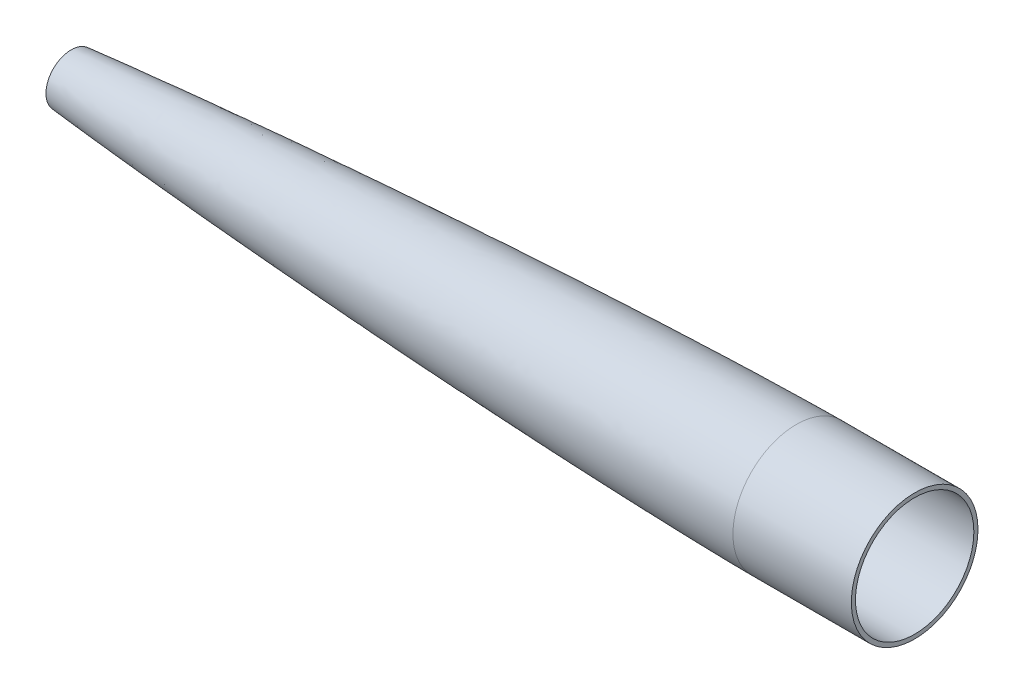
SolidWorks part; units mm, degrees
ref_plane "Front Plane" through (0, 0, 0) normal (0, 0, 1) x (1, 0, 0)
ref_plane "Top Plane" through (0, 0, 0) normal (0, 1, 0) x (1, 0, 0)
ref_plane "Right Plane" through (0, 0, 0) normal (1, 0, 0) x (0, 0, -1)
sketch "Sketch1" plane through (0, 0, 0) normal (0, 0, 1) x (1, 0, 0)
  line L0 (381, 27.178) -> (431.8, 27.178)
  line L1 (381, 25.4) -> (431.8, 25.4)
  line L2 (431.8, 27.178) -> (431.8, 25.4)
  line L3 (0, 0) -> (-1.5257, 0)
  line L4 (-1.5257, 0) -> (-1.5257, 0.9131)
  spline S0 degree 4 poles (0, 0) (0.0019, 0.0032) (0.0064, 0.0093) (0.0177, 0.0192) (0.0422, 0.0365) (0.0779, 0.0573) (0.1247, 0.0811) (0.1912, 0.1116) (0.271, 0.1447) (0.3911, 0.1908) (0.5706, 0.2533) (0.8326, 0.3363) (1.2601, 0.4592) (1.9831, 0.6462) (3.2808, 0.9439) (5.7051, 1.4307) (10.2743, 2.2232) (18.4903, 3.4427) (31.84, 5.1375) (49.7469, 7.0995) (71.1098, 9.1678) (94.2686, 11.1851) (117.4416, 13.0306) (140.6255, 14.7331) (163.8183, 16.3102) (187.0185, 17.7729) (210.2253, 19.1277) (239.2412, 20.6903) (268.266, 22.0787) (297.2989, 23.2863) (326.3397, 24.2853) (346.2421, 24.8431) (362.8124, 25.1993) (373.5739, 25.3501) (378.5246, 25.3942) (381, 25.4) knots 0 0 0 0 0 0.000039 0.000078 0.000157 0.000314 0.000471 0.000628 0.000923 0.001218 0.001818 0.002616 0.0038 0.005873 0.009633 0.01655 0.029679 0.054408 0.096565 0.157395 0.218224 0.279054 0.339884 0.400713 0.461543 0.522372 0.583202 0.644031 0.765691 0.82652 0.88735 0.948179 0.97409 1 1 1 1 1 construction
  spline S1 degree 4 poles (0, 0) (0.0019, 0.0032) (0.0064, 0.0093) (0.0177, 0.0192) (0.0422, 0.0365) (0.0779, 0.0573) (0.1247, 0.0811) (0.1912, 0.1116) (0.271, 0.1447) (0.3911, 0.1908) (0.5706, 0.2533) (0.8326, 0.3363) (1.2601, 0.4592) (1.9831, 0.6462) (3.2808, 0.9439) (5.7051, 1.4307) (10.2743, 2.2232) (18.4903, 3.4427) (31.84, 5.1375) (49.7469, 7.0995) (71.1098, 9.1678) (94.2686, 11.1851) (117.4416, 13.0306) (140.6255, 14.7331) (163.8183, 16.3102) (187.0185, 17.7729) (210.2253, 19.1277) (239.2412, 20.6903) (268.266, 22.0787) (297.2989, 23.2863) (326.3397, 24.2853) (346.2421, 24.8431) (362.8124, 25.1993) (373.5739, 25.3501) (378.5246, 25.3942) (381, 25.4) knots 0 0 0 0 0 0.000039 0.000078 0.000157 0.000314 0.000471 0.000628 0.000923 0.001218 0.001818 0.002616 0.0038 0.005873 0.009633 0.01655 0.029679 0.054408 0.096565 0.157395 0.218224 0.279054 0.339884 0.400713 0.461543 0.522372 0.583202 0.644031 0.765691 0.82652 0.88735 0.948179 0.97409 1 1 1 1 1
  spline S2 degree 1 poles (-1.5257, 0.9131) (381, 27.178) knots 0 0 1 1 construction
  spline S3 degree 3 poles (-1.5257, 0.9131) (-1.4569, 1.028) (-1.2638, 1.2699) (-1.0874, 1.4122) (-1.0135, 1.4682) (-0.9258, 1.5282) (-0.8554, 1.5714) (-0.781, 1.6138) (-0.7219, 1.6452) (-0.652, 1.6803) (-0.5784, 1.7149) (-0.5005, 1.7492) (-0.4055, 1.789) (-0.2986, 1.8307) (-0.1799, 1.8743) (-0.0293, 1.9267) (0.1485, 1.9847) (0.3542, 2.0477) (0.6217, 2.1254) (0.9478, 2.2143) (1.333, 2.3128) (1.8409, 2.4362) (2.4702, 2.5796) (3.2199, 2.7399) (4.2165, 2.9424) (5.4577, 3.1787) (6.9445, 3.4446) (8.4301, 3.6966) (9.9145, 3.9378) (11.8933, 4.2478) (14.3668, 4.6164) (17.3349, 5.0357) (20.3031, 5.4369) (24.2616, 5.9518) (29.2112, 6.5629) (35.1525, 7.2565) (41.0957, 7.9184) (49.0223, 8.7645) (58.9341, 9.764) (70.8331, 10.8911) (82.7362, 11.9575) (94.6427, 12.972) (106.5523, 13.9408) (122.4353, 15.1775) (142.2951, 16.629) (166.135, 18.2394) (189.9821, 19.7296) (213.8356, 21.1064) (245.6483, 22.7946) (285.4289, 24.6294) (325.227, 26.0608) (353.1023, 26.7817) (369.0324, 27.0705) (377.0118, 27.1686) (381, 27.178) knots 0 0 0 0 0.000031 0.000061 0.000092 0.000122 0.000183 0.000244 0.000305 0.000366 0.000488 0.00061 0.000732 0.000977 0.001221 0.001465 0.001953 0.002441 0.00293 0.003906 0.004883 0.005859 0.007813 0.009766 0.011719 0.015625 0.019531 0.023438 0.027344 0.03125 0.039063 0.046876 0.054688 0.062501 0.078126 0.093751 0.109376 0.125001 0.156252 0.187502 0.218752 0.250003 0.281253 0.312503 0.375004 0.437505 0.500005 0.562506 0.625007 0.750008 0.87501 0.93751 0.968761 1.000011 1.000011 1.000011 1.000011
  dimension "D1" = 50.8
  dimension "D2" = 381
  dimension "D3" = 1.778
revolve "Revolve1" add sketch "Sketch1" angle 360 about L3
ref_plane "Plane1" through (69.85, 0, 0) normal (1, 0, 0) x (0, 0, -1)
split "Split1" trim tools "Plane1" bodies to split 101 resulting bodies 102
